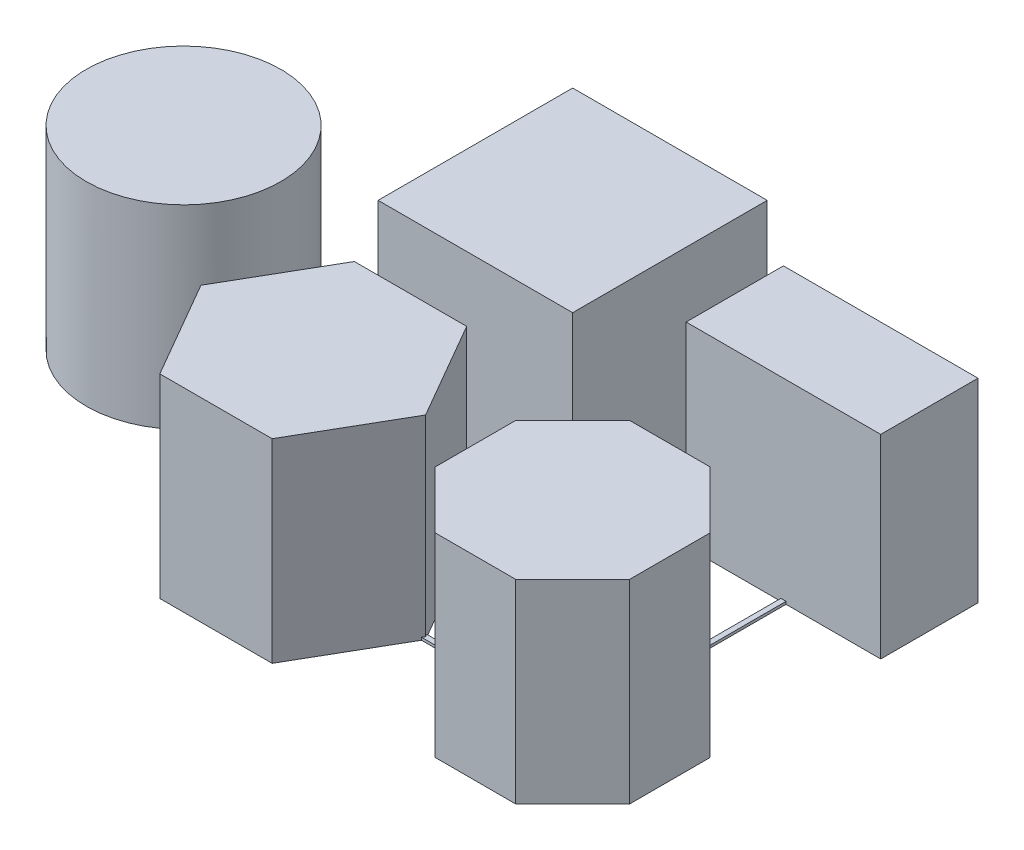
SolidWorks part; units mm, degrees
ref_plane "Ebene vorne" through (0, 0, 0) normal (0, 0, 1) x (1, 0, 0)
ref_plane "Ebene oben" through (0, 0, 0) normal (0, 1, 0) x (1, 0, 0)
ref_plane "Ebene rechts" through (0, 0, 0) normal (1, 0, 0) x (0, 0, -1)
sketch "Skizze1" plane through (0, 0, 0) normal (0, 1, 0) x (1, 0, 0)
  line L1 (15, 5) -> (45, 5)
  line L2 (15, 5) -> (15, 35)
  line L3 (15, 35) -> (45, 35)
  line L4 (45, 5) -> (45, 35)
  line L5 (15, 5) -> (45, 35) construction
  line L6 (15, 35) -> (45, 5) construction
  line L7 (38.6603, -5) -> (21.3397, -5)
  line L8 (21.3397, -5) -> (12.6795, -20)
  line L9 (12.6795, -20) -> (21.3397, -35)
  line L10 (21.3397, -35) -> (38.6603, -35)
  line L11 (38.6603, -35) -> (47.3205, -20)
  line L12 (47.3205, -20) -> (38.6603, -5)
  line L13 (55, 12.5) -> (85, 12.5)
  line L14 (55, 12.5) -> (55, 27.5)
  line L15 (55, 27.5) -> (85, 27.5)
  line L16 (85, 12.5) -> (85, 27.5)
  line L17 (55, 12.5) -> (85, 27.5) construction
  line L18 (55, 27.5) -> (85, 12.5) construction
  line L19 (76.2132, -5) -> (63.7868, -5)
  line L20 (63.7868, -5) -> (55, -13.7868)
  line L21 (55, -13.7868) -> (55, -26.2132)
  line L22 (55, -26.2132) -> (63.7868, -35)
  line L23 (63.7868, -35) -> (76.2132, -35)
  line L24 (76.2132, -35) -> (85, -26.2132)
  line L25 (85, -26.2132) -> (85, -13.7868)
  line L26 (85, -13.7868) -> (76.2132, -5)
  circle A0 centre (-10, 0) radius 15
  circle A1 centre (30, -20) radius 15 construction
  circle A2 centre (70, -20) radius 15 construction
  point P2 (30, 20)
  point P16 (70, 20)
  point P17 (-10, 13.8041)
  dimension "D1" = 30
  dimension "D2" = 30
  dimension "D3" = 30
  dimension "D4" = 10
  dimension "D5" = 5
  dimension "D7" = 40
  dimension "D8" = 10
  dimension "D10" = 30
  dimension "D11" = 15
  dimension "D12" = 40
  dimension "D13" = 30
  dimension "D14" = 40
extrude "Aufsatz-Linear austragen1" add sketch "Skizze1" along normal blind 30
sketch "Skizze2" plane through (0, 0, 0) normal (0, -1, 0) x (1, 0, 0)
  line L6 (30, 20) -> (-10, 0)
  line L11 (-10, 0) -> (30, -20)
  line L14 (15, -35) -> (45, -5) construction
  line L15 (30, -20) -> (70, -20)
  line L16 (55, -27.5) -> (85, -12.5) construction
  line L17 (70, -20) -> (70, 20)
  line L18 (70, 20) -> (30, 20)
extrude "Linear-Austragen-Dünn1" add sketch "Skizze2" against normal blind 0.4 thin thin type mid plane wall 0.8
ref_plane "Ebene1" [suppressed] through (55, 0, 0) normal (-1, 0, 0) x (0, 0, 1)
other "Schneiden1" [suppressed]
